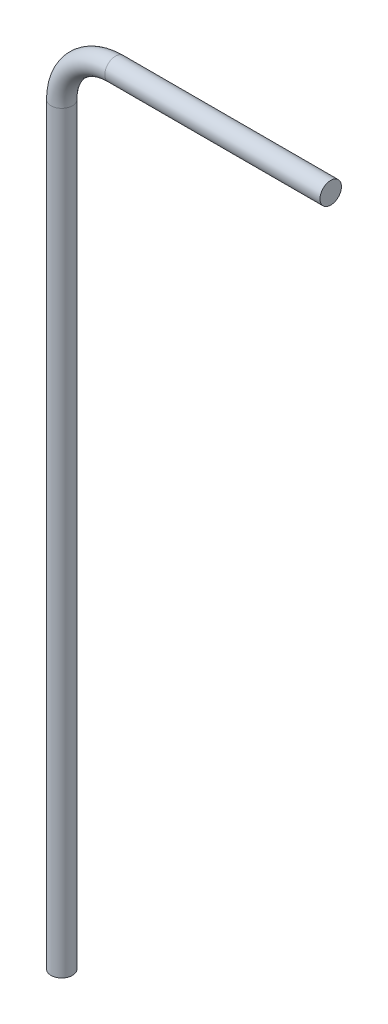
SolidWorks part; units mm, degrees
ref_plane "Front Plane" through (0, 0, 0) normal (0, 0, 1) x (1, 0, 0)
ref_plane "Top Plane" through (0, 0, 0) normal (0, 1, 0) x (1, 0, 0)
ref_plane "Right Plane" through (0, 0, 0) normal (1, 0, 0) x (0, 0, -1)
sketch "Sketch1" plane through (0, 0, 0) normal (0, 0, 1) x (1, 0, 0)
  line L0 (0, -89.0692) -> (0, 50.9308)
  line L1 (10, 60.9308) -> (50, 60.9308)
  arc A0 (0, 50.9308) -> (10, 60.9308) centre (10, 50.9308) cw
  point P6 (0, 60.9308)
  dimension "D3" = 10
  dimension "D1" = 150
  dimension "D2" = 50
ref_plane "Plane1" through (50, 0, 0) normal (1, 0, 0) x (0, 0, -1)
sketch "Sketch2" plane through (50, 0, 0) normal (1, 0, 0) x (0, 0, -1)
  circle A0 centre (0, 60.9308) radius 2
  dimension "D1" = 4
sweep "Sweep1" add profiles "Sketch2" path "Sketch1"
